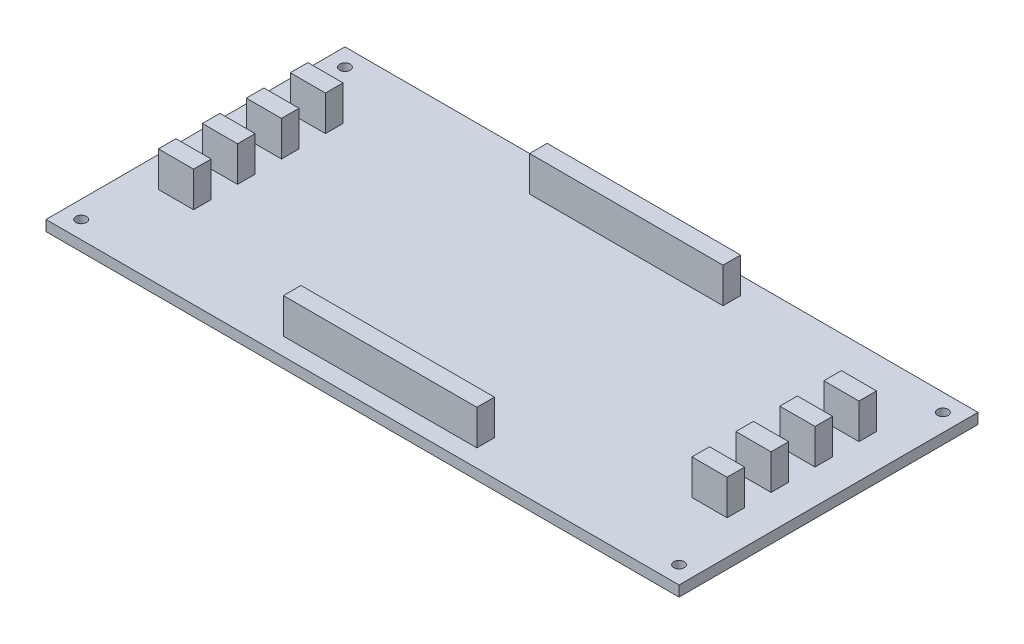
SolidWorks part; units mm, degrees
ref_plane "Face" through (0, 0, 0) normal (0, 0, 1) x (1, 0, 0)
ref_plane "Dessus" through (0, 0, 0) normal (0, 1, 0) x (1, 0, 0)
ref_plane "Droite" through (0, 0, 0) normal (1, 0, 0) x (0, 0, -1)
sketch "Esquisse1" plane through (0, 0, 0) normal (0, 1, 0) x (1, 0, 0)
  line L0 (90, 85) -> (90, 0) construction
  line L1 (0, 0) -> (180, 0)
  line L2 (0, 0) -> (0, 85)
  line L3 (0, 85) -> (180, 85)
  line L4 (180, 0) -> (180, 85)
  line L5 (0, 42.5) -> (180, 42.5) construction
  circle A0 centre (5, 80) radius 1.5
  circle A1 centre (175, 80) radius 1.5
  circle A2 centre (175, 5) radius 1.5
  circle A3 centre (5, 5) radius 1.5
  dimension "D3" = 3
  dimension "D1" = 85
  dimension "D2" = 180
  dimension "D4" = 5
  dimension "D5" = 5
extrude "Extrusion1" add sketch "Esquisse1" along normal blind 3
sketch "Esquisse2" plane through (0, 3, 0) normal (0, 1, 0) x (1, 0, 0)
  line L0 (62.5, 80) -> (62.5, 5) construction
  line L1 (62.5, 80) -> (117.5, 80)
  line L2 (62.5, 80) -> (62.5, 75)
  line L3 (62.5, 75) -> (117.5, 75)
  line L4 (117.5, 80) -> (117.5, 75)
  line L5 (62.5, 10) -> (117.5, 10)
  line L6 (62.5, 10) -> (62.5, 5)
  line L7 (62.5, 5) -> (117.5, 5)
  line L8 (117.5, 10) -> (117.5, 5)
  line L10 (117.5, 80) -> (117.5, 5) construction
  line L12 (90, 85) -> (90, 0) construction
  line L13 (180, 85) -> (0, 85) construction
  line L14 (0, 0) -> (180, 0) construction
  line L15 (0, 42.5) -> (180, 42.5) construction
  line L16 (0, 85) -> (0, 0) construction
  line L17 (180, 0) -> (180, 85) construction
  point P20 (62.5, 42.5)
  point P21 (90, 75)
  dimension "D1" = 65
  dimension "D2" = 5
  dimension "D4" = 55
extrude "Extrusion2" add sketch "Esquisse2" along normal blind 10
sketch "Esquisse4" plane through (0, 3, 0) normal (0, 1, 0) x (1, 0, 0)
  line L0 (160.2951, 65.8623) -> (170.2951, 65.8623)
  line L1 (8.5938, 65.8623) -> (18.5938, 65.8623)
  line L2 (8.5938, 65.8623) -> (8.5938, 60.8623)
  line L3 (8.5938, 60.8623) -> (18.5938, 60.8623)
  line L4 (18.5938, 65.8623) -> (18.5938, 60.8623)
  line L5 (8.5938, 40.8623) -> (18.5938, 40.8623)
  line L6 (8.5938, 40.8623) -> (8.5938, 35.8623)
  line L7 (8.5938, 35.8623) -> (18.5938, 35.8623)
  line L8 (18.5938, 40.8623) -> (18.5938, 35.8623)
  line L9 (8.5938, 28.3623) -> (18.5938, 28.3623)
  line L10 (8.5938, 28.3623) -> (8.5938, 23.3623)
  line L11 (8.5938, 23.3623) -> (18.5938, 23.3623)
  line L12 (18.5938, 28.3623) -> (18.5938, 23.3623)
  line L13 (8.5938, 53.3623) -> (18.5938, 53.3623)
  line L14 (8.5938, 53.3623) -> (8.5938, 48.3623)
  line L15 (8.5938, 48.3623) -> (18.5938, 48.3623)
  line L16 (18.5938, 53.3623) -> (18.5938, 48.3623)
  line L17 (160.2951, 65.8623) -> (160.2951, 60.8623)
  line L18 (160.2951, 60.8623) -> (170.2951, 60.8623)
  line L19 (170.2951, 65.8623) -> (170.2951, 60.8623)
  line L20 (160.2951, 40.8623) -> (170.2951, 40.8623)
  line L21 (160.2951, 40.8623) -> (160.2951, 35.8623)
  line L22 (160.2951, 35.8623) -> (170.2951, 35.8623)
  line L23 (170.2951, 40.8623) -> (170.2951, 35.8623)
  line L24 (160.2951, 28.3623) -> (170.2951, 28.3623)
  line L25 (160.2951, 28.3623) -> (160.2951, 23.3623)
  line L26 (160.2951, 23.3623) -> (170.2951, 23.3623)
  line L27 (170.2951, 28.3623) -> (170.2951, 23.3623)
  line L28 (160.2951, 53.3623) -> (170.2951, 53.3623)
  line L29 (160.2951, 53.3623) -> (160.2951, 48.3623)
  line L30 (160.2951, 48.3623) -> (170.2951, 48.3623)
  line L31 (170.2951, 53.3623) -> (170.2951, 48.3623)
  dimension "D1" = 10
  dimension "D2" = 5
  dimension "D3" = 7.5
  dimension "D4" = 7.5
  dimension "D5" = 7.5
  dimension "D6" = 10
  dimension "D7" = 5
  dimension "D8" = 7.5
  dimension "D9" = 7.5
  dimension "D10" = 7.5
extrude "Extrusion4" add sketch "Esquisse4" along normal blind 10
